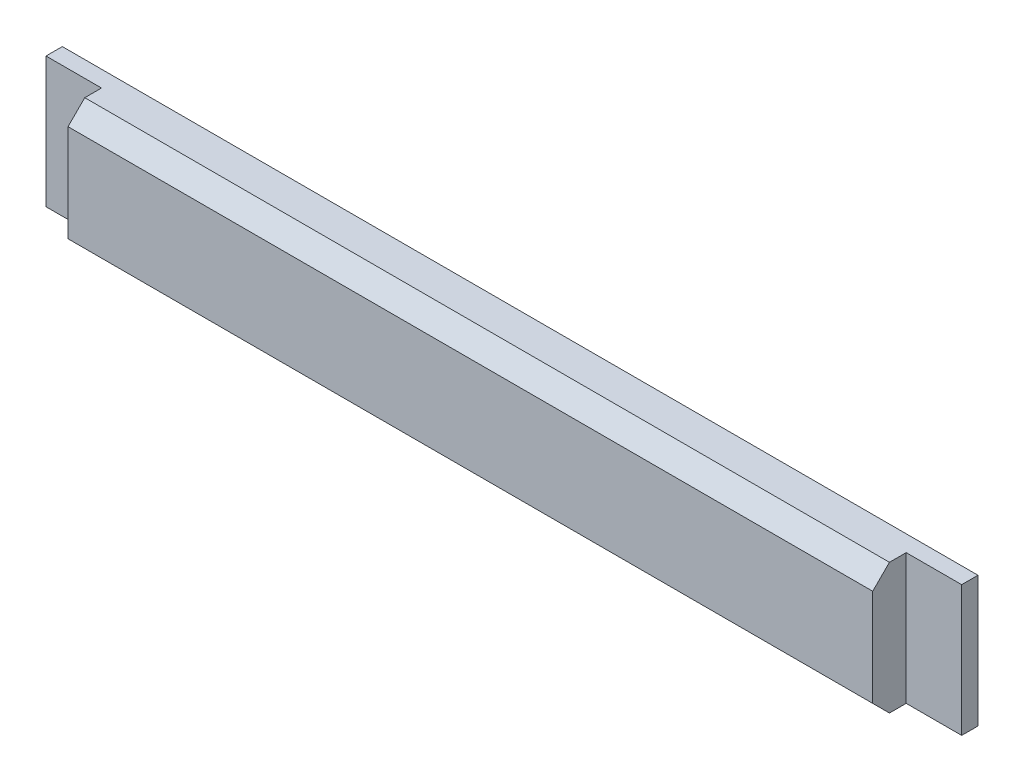
SolidWorks part; units mm, degrees
ref_plane "Plan de face" through (0, 0, 0) normal (0, 0, 1) x (1, 0, 0)
ref_plane "Plan de dessus" through (0, 0, 0) normal (0, 1, 0) x (1, 0, 0)
ref_plane "Plan de droite" through (0, 0, 0) normal (1, 0, 0) x (0, 0, -1)
sketch "Esquisse1" plane through (0, 0, 0) normal (0, 0, 1) x (1, 0, 0)
  line L0 (142.4148, 185.3139) -> (142.4148, 97.8139) construction
  line L1 (-138.0852, 97.8139) -> (142.4148, 97.8139)
  line L2 (-138.0852, 97.8139) -> (-138.0852, 137.8139)
  line L3 (-138.0852, 137.8139) -> (142.4148, 137.8139)
  line L4 (142.4148, 97.8139) -> (142.4148, 137.8139)
  dimension "D1" = 0
  dimension "D2" = 40
extrude "Boss.-Extru.1" add sketch "Esquisse1" along normal up to surface (5 mm away)
sketch "Esquisse2" plane through (0, 0, 5) normal (0, 0, 1) x (1, 0, 0)
  line L0 (142.4148, 137.8139) -> (-138.0852, 137.8139) construction
  line L1 (-121.0852, 137.8139) -> (125.4148, 137.8139)
  line L2 (-121.0852, 137.8139) -> (-121.0852, 97.8139)
  line L3 (-121.0852, 97.8139) -> (125.4148, 97.8139)
  line L4 (125.4148, 137.8139) -> (125.4148, 97.8139)
  line L5 (-138.0852, 97.8139) -> (142.4148, 97.8139) construction
  line L6 (127.4148, 97.8139) -> (127.4148, 185.3139) construction
  line L7 (-123.0852, 185.3139) -> (-123.0852, 97.8139) construction
  dimension "D1" = 2
  dimension "D2" = 2
extrude "Boss.-Extru.2" add sketch "Esquisse2" along normal blind 10.25
sketch "Esquisse3" plane through (-121.0852, 0, 0) normal (-1, 0, 0) x (0, 0, 1)
  line L0 (10.125, 137.8139) -> (15.25, 137.8139)
  line L1 (15.25, 137.8139) -> (5, 137.8139) construction
  line L2 (15.25, 137.8139) -> (15.25, 132.6889)
  line L3 (15.25, 137.8139) -> (15.25, 97.8139) construction
  line L4 (15.25, 132.6889) -> (10.125, 137.8139)
  line L5 (15.25, 97.8139) -> (15.25, 102.9389)
  line L6 (15.25, 102.9389) -> (10.125, 97.8139)
  line L7 (15.25, 97.8139) -> (5, 97.8139) construction
  line L8 (10.125, 97.8139) -> (15.25, 97.8139)
extrude "Enlèv. mat.-Extru.1" cut sketch "Esquisse3" against normal up to next
